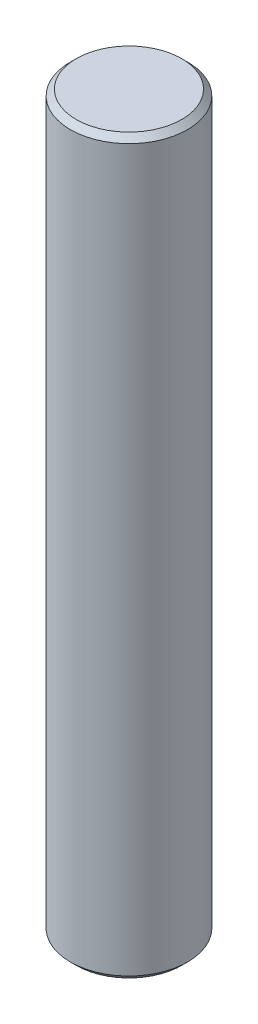
SolidWorks part; units mm, degrees
material "普通碳钢"
ref_plane "前视基准面" through (0, 0, 0) normal (0, 0, 1) x (1, 0, 0)
ref_plane "上视基准面" through (0, 0, 0) normal (0, 1, 0) x (1, 0, 0)
ref_plane "右视基准面" through (0, 0, 0) normal (1, 0, 0) x (0, 0, -1)
sketch "草图1" plane through (0, 0, 0) normal (0, 1, 0) x (1, 0, 0)
  circle A0 centre (0, 0) radius 2
  dimension "D1" = 4
extrude "凸台-拉伸1" add sketch "草图1" along normal blind 25
chamfer "倒角1" distance 0.2 angle 45 2 edges at (0, 25, 2) (0, 0, 2)
